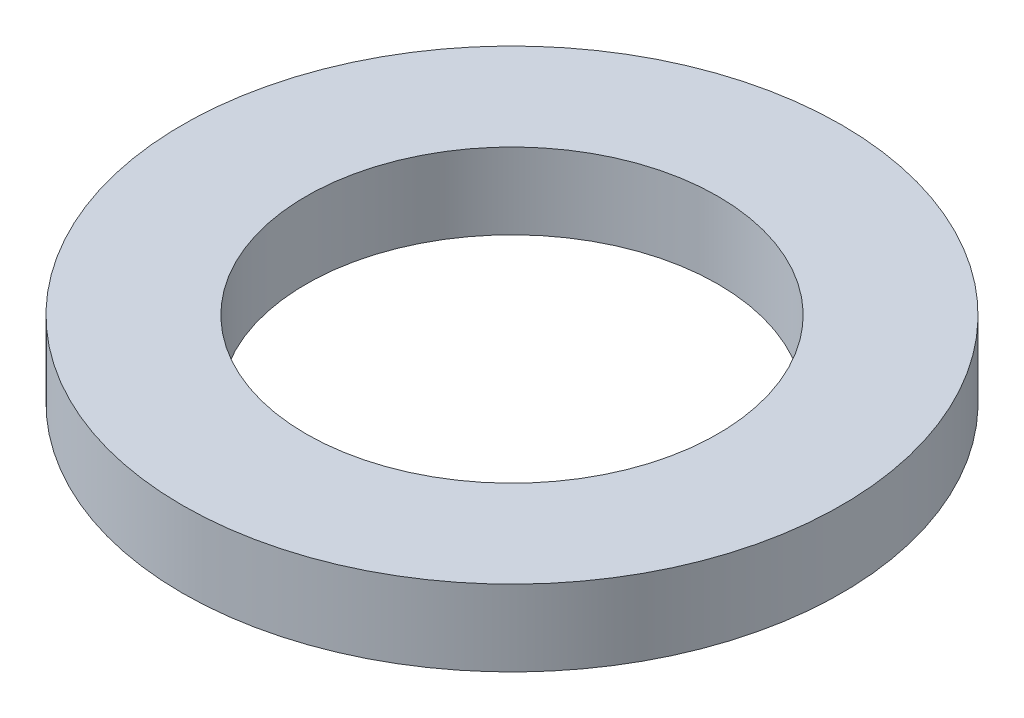
SolidWorks part; units mm, degrees
ref_plane "Front Plane" through (0, 0, 0) normal (0, 0, 1) x (1, 0, 0)
ref_plane "Top Plane" through (0, 0, 0) normal (0, 1, 0) x (1, 0, 0)
ref_plane "Right Plane" through (0, 0, 0) normal (1, 0, 0) x (0, 0, -1)
sketch "Sketch1" plane through (0, 0, 0) normal (0, 1, 0) x (1, 0, 0)
  circle A0 centre (0, 0) radius 16.65
  circle A1 centre (0, 0) radius 26.65
  point P3 (0, 0)
  dimension "D1" = 33.3
  dimension "D2" = 10
extrude "Boss-Extrude1" add sketch "Sketch1" along normal blind 6.15
